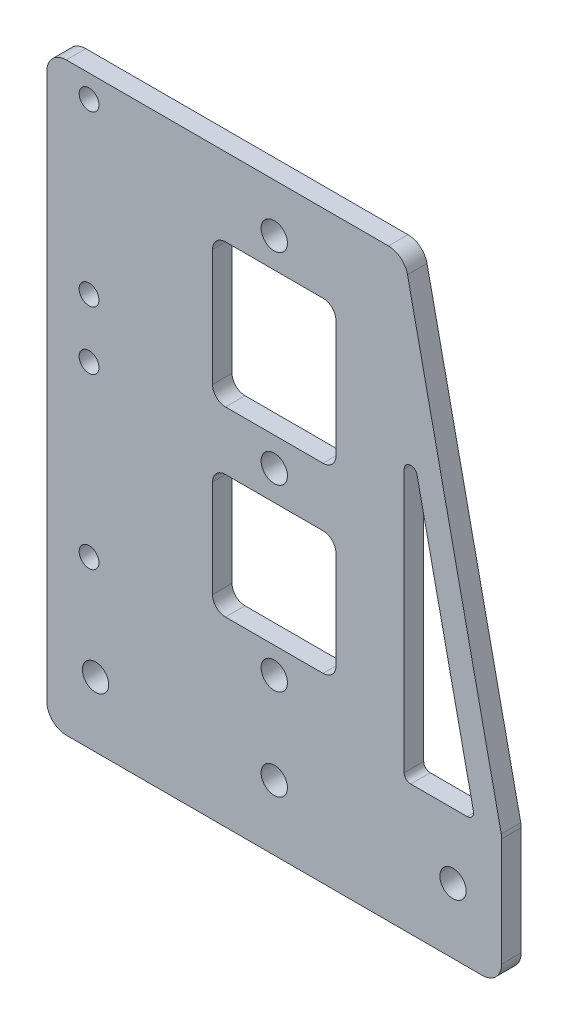
SolidWorks part; units mm, degrees
material "Thornel Mat VMA"
ref_plane "前视基准面" through (0, 0, 0) normal (0, 0, 1) x (1, 0, 0)
ref_plane "上视基准面" through (0, 0, 0) normal (0, 1, 0) x (1, 0, 0)
ref_plane "右视基准面" through (0, 0, 0) normal (1, 0, 0) x (0, 0, -1)
other "Configuration Table"
sketch "草图1" plane through (0, 0, 0) normal (0, 0, 1) x (1, 0, 0)
  line L0 (0, 0) -> (-70, 0)
  line L1 (-70, 0) -> (-70, 20)
  line L2 (-70, 20) -> (-55, 90)
  line L3 (-55, 90) -> (-15, 90)
  line L4 (-15, 90) -> (0, 20)
  line L5 (0, 20) -> (0, 0)
  point P8 (-35, 90)
  point P9 (-35, 0)
  dimension "D1" = 40
  dimension "D2" = 70
  dimension "D3" = 90
  dimension "D4" = 20
extrude "凸台-拉伸1" add sketch "草图1" along normal blind 3
sketch "草图3" plane through (0, 0, 3) normal (0, 0, 1) x (1, 0, 0)
  line L0 (-35, 90) -> (-35, 0) construction
  line L1 (-44.5, 56) -> (-25.5, 56)
  line L2 (-44.5, 56) -> (-44.5, 78)
  line L3 (-44.5, 78) -> (-25.5, 78)
  line L4 (-25.5, 56) -> (-25.5, 78)
  line L5 (-44.5, 56) -> (-25.5, 78) construction
  line L6 (-44.5, 78) -> (-25.5, 56) construction
  line L7 (-44.5, 28) -> (-25.5, 28)
  line L8 (-44.5, 28) -> (-44.5, 47)
  line L9 (-44.5, 47) -> (-25.5, 47)
  line L10 (-25.5, 28) -> (-25.5, 47)
  line L11 (-44.5, 28) -> (-25.5, 47) construction
  line L12 (-44.5, 47) -> (-25.5, 28) construction
  line L13 (-15, 90) -> (-55, 90) construction
  line L14 (-70, 0) -> (0, 0) construction
  line L15 (-55, 70.9096) -> (-55, 20) construction
  line L16 (-55, 20) -> (-65.9092, 20) construction
  line L17 (-65.9092, 20) -> (-55, 70.9096) construction
  line L18 (-55, 90) -> (-70, 20) construction
  line L19 (-4.0908, 20) -> (-15, 70.9096)
  line L20 (-15, 20) -> (-4.0908, 20)
  line L21 (-15, 70.9096) -> (-15, 20)
  point P0 (-35, 67)
  point P5 (-35, 37.5)
  dimension "D1" = 19
  dimension "D2" = 28
  dimension "D3" = 4
  dimension "D4" = 20
  dimension "D5" = 12
  dimension "D6" = 22
extrude "切除-拉伸1" cut sketch "草图3" against normal blind 3
fillet "圆角1" radius 1 3 edges at (-15, 70.9096, 1.5) (-4.0908, 20, 1.5) (-15, 20, 1.5)
fillet "圆角2" radius 2 8 edges at (-25.5, 56, 1.5) (-44.5, 56, 1.5) (-44.5, 78, 1.5) (-25.5, 78, 1.5) (-25.5, 28, 1.5) (-44.5, 47, 1.5) (-25.5, 47, 1.5) (-44.5, 28, 1.5)
sketch "草图4" plane through (0, 0, 3) normal (0, 0, 1) x (1, 0, 0)
  line L0 (-70, 0) -> (0, 0) construction
  line L1 (-35, 28) -> (-35, 10) construction
  line L2 (-42.5, 28) -> (-27.5, 28) construction
  circle A0 centre (-62.5, 10) radius 2.025
  circle A1 centre (-35, 10) radius 2.025
  circle A2 centre (-7.5, 10) radius 2.025
  dimension "D2" = 4.05
  dimension "D3" = 55
  dimension "D1" = 10
extrude "切除-拉伸2" cut sketch "草图4" against normal blind 3
sketch "草图5" plane through (0, 0, 0) normal (0, 0, -1) x (-1, 0, 0)
  circle A0 centre (35, 82.567) radius 2.025
  circle A1 centre (35, 51.567) radius 2.025
  circle A2 centre (35, 24) radius 2.025
  circle A3 centre (35, 82.567) radius 2.025 construction
  circle A4 centre (35, 51.567) radius 2.025 construction
  circle A5 centre (35, 24) radius 2.025 construction
  dimension "D1" = 4.05
extrude "切除-拉伸3" cut sketch "草图5" against normal blind 10
sketch "草图7" plane through (0, 0, 3) normal (0, 0, 1) x (1, 0, 0)
  line L0 (-55, 90) -> (-70, 90)
  line L1 (-70, 90) -> (-70, 20)
  line L2 (-55, 90) -> (-70, 20) construction
  line L3 (-55, 90) -> (-70, 20)
extrude "凸台-拉伸2" add sketch "草图7" against normal up to surface (3 mm away) up to face at (-37.025, 82.567, 0)
fillet "圆角3" radius 3 5 edges at (0, 20, 1.5) (-15, 90, 1.5) (-70, 0, 1.5) (0, 0, 1.5) (-70, 90, 1.5)
sketch "草图8" plane through (0, 0, 3) normal (0, 0, 1) x (1, 0, 0)
  circle A0 centre (-63.5, 86.5) radius 1.525
  circle A1 centre (-63.5, 60.5) radius 1.525
  circle A2 centre (-63.5, 51.5) radius 1.525
  circle A3 centre (-63.5, 25.5) radius 1.525
  circle A4 centre (-63.5, 86.5) radius 1.525 construction
  circle A5 centre (-63.5, 60.5) radius 1.525 construction
  circle A6 centre (-63.5, 51.5) radius 1.525 construction
  circle A7 centre (-63.5, 25.5) radius 1.525 construction
  dimension "D1" = 3.05
extrude "切除-拉伸4" cut sketch "草图8" against normal through all both
